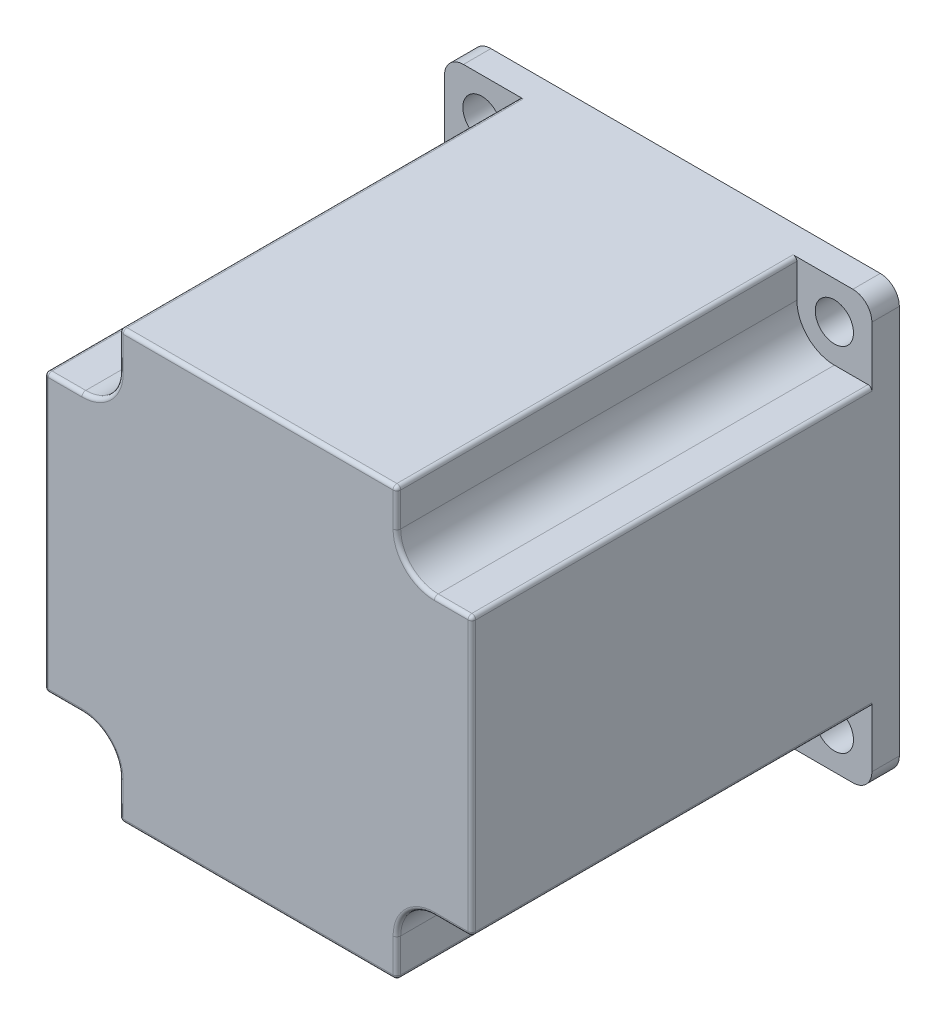
SolidWorks part; units mm, degrees
ref_plane "Front Plane" through (0, 0, 0) normal (0, 0, 1) x (1, 0, 0)
ref_plane "Top Plane" through (0, 0, 0) normal (0, 1, 0) x (1, 0, 0)
ref_plane "Right Plane" through (0, 0, 0) normal (1, 0, 0) x (0, 0, -1)
sketch "Sketch1" plane through (0, 0, 0) normal (0, 0, 1) x (1, 0, 0)
  line L1 (-28.5, -28.5) -> (28.5, -28.5)
  line L2 (-28.5, -28.5) -> (-28.5, 28.5)
  line L3 (-28.5, 28.5) -> (28.5, 28.5)
  line L4 (28.5, -28.5) -> (28.5, 28.5)
  line L5 (-28.5, -28.5) -> (28.5, 28.5) construction
  line L6 (-28.5, 28.5) -> (28.5, -28.5) construction
  point P0 (0, 0)
  dimension "D1" = 57
  dimension "D2" = 57
extrude "Boss-Extrude1" add sketch "Sketch1" along normal blind 57
sketch "Sketch2" plane through (0, 0, 57) normal (0, 0, 1) x (1, 0, 0)
  line L0 (-28.5, 28.5) -> (28.5, -28.5) construction
  line L2 (-23.5, -23.5) -> (23.5, -23.5) construction
  line L3 (-23.5, -23.5) -> (-23.5, 23.5) construction
  line L4 (-23.5, 23.5) -> (23.5, 23.5) construction
  line L5 (23.5, -23.5) -> (23.5, 23.5) construction
  line L6 (-23.5, -23.5) -> (23.5, 23.5) construction
  line L7 (-23.5, 23.5) -> (23.5, -23.5) construction
  circle A0 centre (-23.5, 23.5) radius 2.55
  circle A1 centre (23.5, 23.5) radius 2.55
  circle A2 centre (23.5, -23.5) radius 2.55
  circle A3 centre (-23.5, -23.5) radius 2.55
  point P4 (0, 0)
  dimension "D2" = 5.1
  dimension "D1" = 47
extrude "Cut-Extrude1" cut sketch "Sketch2" against normal through all
sketch "Sketch3" plane through (0, 0, 57) normal (0, 0, 1) x (1, 0, 0)
  line L0 (-18.5, 23.5) -> (-18.5, 28.5)
  line L1 (28.5, 28.5) -> (-28.5, 28.5) construction
  line L2 (-23.5, 18.5) -> (-28.5, 18.5)
  line L3 (-28.5, 28.5) -> (-28.5, -28.5) construction
  line L4 (0, 28.5) -> (0, -28.5) construction
  line L5 (-28.5, -28.5) -> (28.5, -28.5) construction
  line L6 (-28.5, 0) -> (28.5, 0) construction
  line L7 (28.5, -28.5) -> (28.5, 28.5) construction
  line L8 (-18.5, 28.5) -> (-28.5, 28.5)
  line L9 (-28.5, 28.5) -> (-28.5, 18.5)
  line L10 (28.5, 28.5) -> (28.5, 18.5)
  line L11 (18.5, 28.5) -> (28.5, 28.5)
  line L12 (23.5, 18.5) -> (28.5, 18.5)
  line L13 (18.5, 23.5) -> (18.5, 28.5)
  line L14 (-28.5, -28.5) -> (-28.5, -18.5)
  line L15 (-18.5, -28.5) -> (-28.5, -28.5)
  line L16 (-23.5, -18.5) -> (-28.5, -18.5)
  line L17 (-18.5, -23.5) -> (-18.5, -28.5)
  line L18 (18.5, -23.5) -> (18.5, -28.5)
  line L19 (23.5, -18.5) -> (28.5, -18.5)
  line L20 (18.5, -28.5) -> (28.5, -28.5)
  line L21 (28.5, -28.5) -> (28.5, -18.5)
  arc A0 (-23.5, 18.5) -> (-18.5, 23.5) centre (-23.5, 23.5) ccw
  arc A1 (23.5, 18.5) -> (18.5, 23.5) centre (23.5, 23.5) cw
  arc A2 (-23.5, -18.5) -> (-18.5, -23.5) centre (-23.5, -23.5) cw
  arc A3 (23.5, -18.5) -> (18.5, -23.5) centre (23.5, -23.5) ccw
  circle A4 centre (-23.5, 23.5) radius 2.55 construction
  dimension "D2" = 42
extrude "Cut-Extrude2" cut sketch "Sketch3" against normal blind 53.34
sketch "Sketch4" plane through (0, 0, 0) normal (0, 0, -1) x (-1, 0, 0)
  circle A0 centre (0, 0) radius 19.05
  dimension "D1" = 38.1
extrude "Boss-Extrude2" add sketch "Sketch4" along normal blind 1.6
sketch "Sketch5" plane through (0, 0, -1.6) normal (0, 0, -1) x (-1, 0, 0)
  circle A0 centre (0, 0) radius 3.175
  dimension "D1" = 6.35
extrude "Boss-Extrude3" add sketch "Sketch5" along normal blind 19.4
sketch "Sketch7" plane through (0, 0, -21) normal (0, 0, -1) x (-1, 0, 0)
  line L0 (-1.2349, 2.925) -> (-1.2349, -2.925)
  circle A0 centre (0, 0) radius 3.175 construction
  circle A1 centre (0, 0) radius 3.175 construction
  arc A2 (-1.2349, 2.925) -> (-1.2349, -2.925) centre (0, 0) ccw
  dimension "D1" = 5.85
extrude "Cut-Extrude3" cut sketch "Sketch7" against normal blind 15
chamfer "Chamfer1" distance 0.254 angle 60 1 edges at (-3.175, 0, -21)
fillet "Fillet1" radius 2.54 4 edges at (-28.5, -28.5, 1.83) (28.5, -28.5, 1.83) (28.5, 28.5, 1.83) (-28.5, 28.5, 1.83)
fillet "Fillet2" radius 0.508 24 edges at (28.5, -18.5, 30.33) (28.5, 18.5, 30.33) (18.5, 28.5, 30.33) (-18.5, 28.5, 30.33) (-28.5, 18.5, 30.33) (-28.5, -18.5, 30.33) (-18.5, -28.5, 30.33) (18.5, -28.5, 30.33) (26, 18.5, 57) (28.5, 0, 57) (26, -18.5, 57) (19.9645, -19.9645, 57) (18.5, -26, 57) (0, -28.5, 57) (-18.5, -26, 57) (-19.9645, -19.9645, 57) (-26, -18.5, 57) (-28.5, 0, 57) (-26, 18.5, 57) (-19.9645, 19.9645, 57) (-18.5, 26, 57) (0, 28.5, 57) (18.5, 26, 57) (19.9645, 19.9645, 57)
